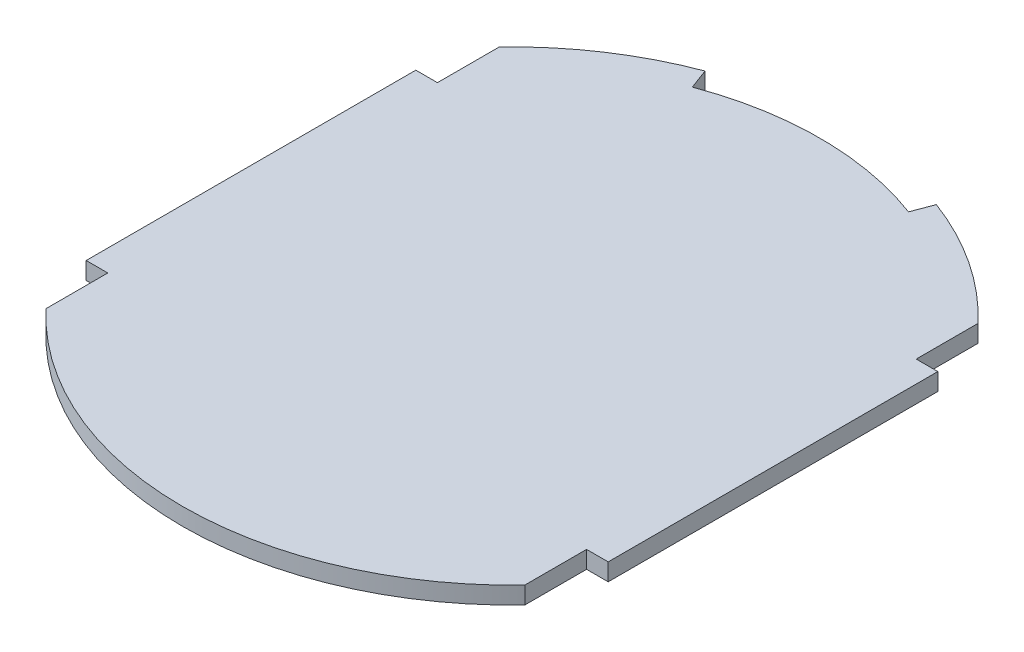
SolidWorks part; units mm, degrees
ref_plane "Front Plane" through (0, 0, 0) normal (0, 0, 1) x (1, 0, 0)
ref_plane "Top Plane" through (0, 0, 0) normal (0, 1, 0) x (1, 0, 0)
ref_plane "Right Plane" through (0, 0, 0) normal (1, 0, 0) x (0, 0, -1)
sketch "Sketch1" plane through (0, 0, 0) normal (0, 1, 0) x (1, 0, 0)
  line L0 (0, 30.5) -> (0, -30.5) construction
  line L1 (-24.15, 15.25) -> (-24.15, -15.25)
  line L2 (30.5, 0) -> (-30.5, 0) construction
  line L3 (-24.15, 15.25) -> (-22.15, 15.25)
  line L4 (24.15, -15.25) -> (24.15, 15.25)
  line L5 (22.15, 15.25) -> (24.15, 15.25)
  line L6 (-24.15, -15.25) -> (-22.15, -15.25)
  line L7 (22.15, 20.9673) -> (22.15, 15.25)
  line L8 (22.15, -15.25) -> (24.15, -15.25)
  line L9 (-22.15, -20.9673) -> (-22.15, -15.25)
  line L10 (22.15, -15.25) -> (22.15, -20.9673)
  line L11 (-22.15, 15.25) -> (-22.15, 20.9673)
  arc A0 (22.15, 20.9673) -> (-22.15, 20.9673) centre (0, 0) ccw
  arc A1 (-22.15, -20.9673) -> (22.15, -20.9673) centre (0, 0) ccw
  dimension "D1" = 61
  dimension "D2" = 48.3
  dimension "D3" = 44.3
  dimension "D4" = 2
  dimension "D5" = 2
  dimension "D6" = 30.5
  dimension "D7" = 2
  dimension "D8" = 2
extrude "Boss-Extrude1" add sketch "Sketch1" along normal blind 1.6
sketch "Sketch2" plane through (0, 1.6, 0) normal (0, 1, 0) x (1, 0, 0)
  line L0 (0, 0) -> (10.7018, 28.5609)
  line L1 (0, 0) -> (-10.7018, 28.5609)
  arc A0 (-10, 26.688) -> (10, 26.688) centre (0, 0) cw
  arc A1 (22.15, 20.9673) -> (-22.15, 20.9673) centre (0, 0) ccw construction
  arc A2 (10.7018, 28.5609) -> (-10.7018, 28.5609) centre (0, 0) ccw
  point P4 (0, 28.5)
  arc M13 (22.15, 20.9673) -> (-22.15, 20.9673) centre (0, 0) ccw
  dimension "D1" = 20
  dimension "D2" = 28.5
extrude "Cut-Extrude1" cut sketch "Sketch2" against normal blind 10 contours L1 A0 L0 M13
